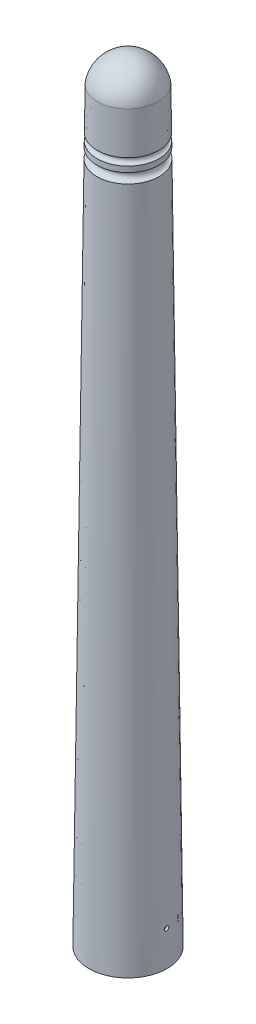
SolidWorks part; units mm, degrees
ref_plane "Plano frontal" through (0, 0, 0) normal (0, 0, 1) x (1, 0, 0)
ref_plane "Plano superior" through (0, 0, 0) normal (0, 1, 0) x (1, 0, 0)
ref_plane "Plano direito" through (0, 0, 0) normal (1, 0, 0) x (0, 0, -1)
ref_plane "Plano1" through (0, 0, 0) normal (0, 0, -1) x (-1, 0, 0)
sketch "Esboço1" plane through (0, 0, 0) normal (0, 0, -1) x (-1, 0, 0)
  line L0 (-4.5, -86) -> (0, -86)
  line L1 (0, -86) -> (0, 3)
  line L2 (-3.5, 0) -> (-3.5562, -4.837)
  line L3 (-3.5659, -5.6655) -> (-3.5733, -6.3081)
  line L4 (-3.5866, -7.4445) -> (-4.5, -86)
  line L5 (0, -86) -> (0, 3) construction
  arc A0 (0, 3) -> (-3.5, 0) centre (0, -0.5417) ccw
  arc A1 (-3.5562, -4.837) -> (-3.5659, -5.6655) centre (-3.5611, -5.2512) cw
  arc A2 (-3.5733, -6.3081) -> (-3.5866, -7.4445) centre (-3.5611, -6.8765) cw
revolve "Revolução1" add sketch "Esboço1" angle 360 about L5
ref_plane "Plano2" through (0, -63.5, 0) normal (0, -1, 0) x (0, 0, 1)
sketch "Esboço2" plane through (0, -63.5, 0) normal (0, -1, 0) x (0, 0, 1)
  line L0 (3.0385, -3.2) -> (-1.5, -3.2)
  line L1 (-1.5, -3.2) -> (-1.5, 3.2)
  line L2 (-1.5, 3.2) -> (3.0385, 3.2)
  arc A0 (3.0385, 3.2) -> (3.0385, -3.2) centre (0, 0) cw
sketch "Esboço3" plane through (0, 0, 0) normal (0, 0, -1) x (-1, 0, 0)
  line L0 (-1.4126, -78.5) -> (0, -78.5)
  line L1 (0, -78.5) -> (0, 0)
  line L2 (-0.5038, -0.3427) -> (-1.4126, -78.5)
  line L3 (0, -78.5) -> (0, 0) construction
  arc A0 (0, 0) -> (-0.5038, -0.3427) centre (0, -0.5417) ccw
revolve "Corte-Revolução1" cut sketch "Esboço3" angle 360 about L3
hole_wizard "Furo1" positions "3DSketch1" profile "Esboço4" legacy
sketch3d "3DSketch1"
  point P0 (-4.4534, -81.9966, 0)
sketch "Esboço4" plane through (-4.4534, -81.9966, 0) normal (0, 0, 1) x (-0.0116, -0.9999, 0)
  line L0 (0, 0) -> (0, 0.3)
  line L1 (0, 0.3) -> (0.255, 0.3)
  line L2 (0.255, 0.3) -> (0.255, 0)
  line L3 (0.255, 0) -> (0, 0)
  line L4 (0, 110) -> (0, -10) construction
  dimension "Diameter" = 0.51
  dimension "Depth" = 0.3
hole_wizard "Furo2" positions "3DSketch2" profile "Esboço5" legacy
sketch3d "3DSketch2"
  point P0 (4.4534, -81.9966, 0)
sketch "Esboço5" plane through (4.4534, -81.9966, 0) normal (0, 0, 1) x (-0.0116, 0.9999, 0)
  line L0 (0, 0) -> (0, 0.3)
  line L1 (0, 0.3) -> (0.255, 0.3)
  line L2 (0.255, 0.3) -> (0.255, 0)
  line L3 (0.255, 0) -> (0, 0)
  line L4 (0, 110) -> (0, -10) construction
  dimension "Diameter" = 0.51
  dimension "Depth" = 0.3
